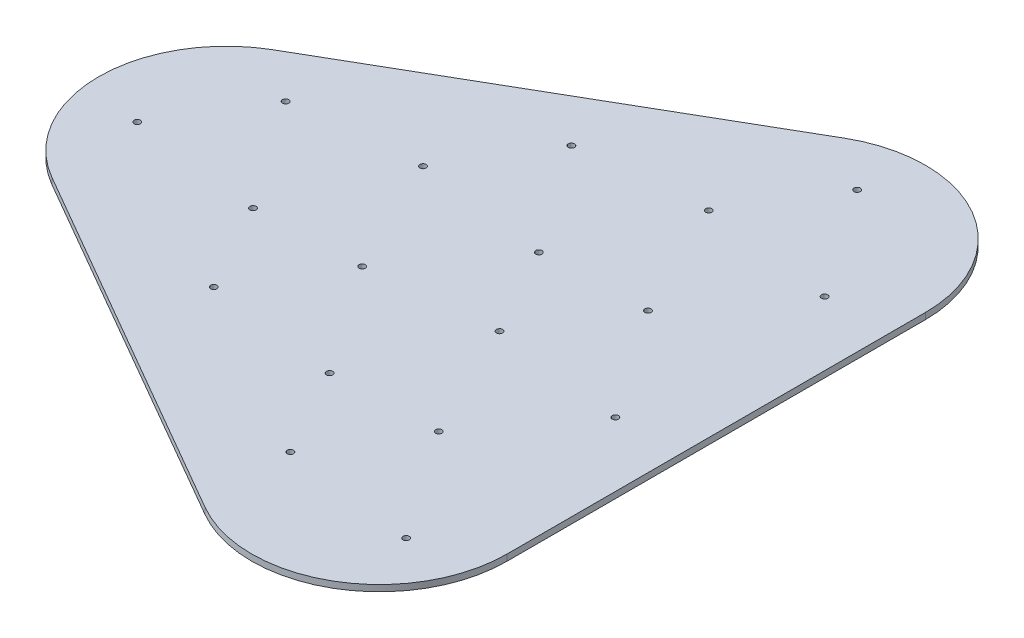
SolidWorks part; units mm, degrees
ref_plane "Front Plane" through (0, 0, 0) normal (0, 0, 1) x (1, 0, 0)
ref_plane "Top Plane" through (0, 0, 0) normal (0, 1, 0) x (1, 0, 0)
ref_plane "Right Plane" through (0, 0, 0) normal (1, 0, 0) x (0, 0, -1)
sketch "Sketch1" plane through (0, 0, 0) normal (0, 1, 0) x (1, 0, 0)
  line L0 (-30.5, 52.8275) -> (142.7051, 152.8275)
  line L1 (234.2051, 100) -> (234.2051, -100)
  line L2 (-30.5, -52.8275) -> (142.7051, -152.8275)
  circle A0 centre (0, 0) radius 41
  circle A1 centre (-6.0777, 34.4683) radius 1.5
  circle A2 centre (-33.02, -9.525) radius 1.5
  circle A3 centre (30.3109, -17.5) radius 1.5
  circle A4 centre (86.6025, -50) radius 41
  circle A5 centre (80.5249, -15.5317) radius 1.5
  circle A6 centre (53.5825, -59.525) radius 1.5
  circle A7 centre (116.9134, -67.5) radius 1.5
  circle A8 centre (86.6025, 50) radius 41
  circle A9 centre (80.5249, 84.4683) radius 1.5
  circle A10 centre (53.5825, 40.475) radius 1.5
  circle A11 centre (116.9134, 32.5) radius 1.5
  circle A12 centre (173.2051, 100) radius 41
  circle A13 centre (167.1274, 134.4683) radius 1.5
  circle A14 centre (140.1851, 90.475) radius 1.5
  circle A15 centre (203.516, 82.5) radius 1.5
  circle A16 centre (173.2051, 0) radius 41
  circle A17 centre (167.1274, 34.4683) radius 1.5
  circle A18 centre (140.1851, -9.525) radius 1.5
  circle A19 centre (203.516, -17.5) radius 1.5
  circle A20 centre (173.2051, -100) radius 41
  circle A21 centre (167.1274, -65.5317) radius 1.5
  circle A22 centre (140.1851, -109.525) radius 1.5
  circle A23 centre (203.516, -117.5) radius 1.5
  circle A24 centre (173.2051, 100) radius 61
  circle A25 centre (173.2051, -100) radius 61
  circle A26 centre (0, 0) radius 61
  dimension "D1" = 6.0777
  dimension "D14" = 82
  dimension "D21" = 82
  dimension "D28" = 82
  dimension "D35" = 82
  dimension "D42" = 82
  dimension "D2" = 34.4683
  dimension "D3" = 9.525
  dimension "D4" = 33.02
  dimension "D5" = 30.3109
  dimension "D6" = 17.5
  dimension "D8" = 34.4683
  dimension "D9" = 6.0777
  dimension "D10" = 9.525
  dimension "D11" = 33.02
  dimension "D12" = 30.3109
  dimension "D13" = 17.5
  dimension "D15" = 34.4683
  dimension "D16" = 6.0777
  dimension "D17" = 9.525
  dimension "D18" = 33.02
  dimension "D19" = 30.3109
  dimension "D20" = 17.5
  dimension "D22" = 34.4683
  dimension "D23" = 6.0777
  dimension "D24" = 9.525
  dimension "D25" = 33.02
  dimension "D26" = 30.3109
  dimension "D27" = 17.5
  dimension "D29" = 34.4683
  dimension "D30" = 6.0777
  dimension "D31" = 9.525
  dimension "D32" = 33.02
  dimension "D33" = 30.3109
  dimension "D34" = 17.5
  dimension "D36" = 34.4683
  dimension "D37" = 6.0777
  dimension "D38" = 9.525
  dimension "D39" = 33.02
  dimension "D40" = 30.3109
  dimension "D41" = 17.5
  dimension "D43" = 100
  dimension "D44" = 100
  dimension "D45" = 100
  dimension "D46" = 50
  dimension "D47" = 100
  dimension "D48" = 100
  dimension "D49" = 100
  dimension "D50" = 100
  dimension "D51" = 100
  dimension "D52" = 100
extrude "Boss-Extrude1" add sketch "Sketch1" along normal blind 3 contours A25 L1 A24 A16 | A16 A25 A4 A20 | A20 A23 A22 A21 | A26 L2 A25 A4 | A26 A4 A25 A16 A24 A8 | A26 A4 A25 A7 A6 A5 | A25 A16 A24 A19 A18 A17 | A12 A15 A14 A13 | A16 A24 A8 A12 | A26 A8 A24 L0 | A26 A8 A24 A11 A10 A9 | A0 A3 A2 A1 | A4 A26 A8 A0 | A16 A25 | A4 A25 | A4 A26 | A8 A26 | A8 A24 | A16 A24
